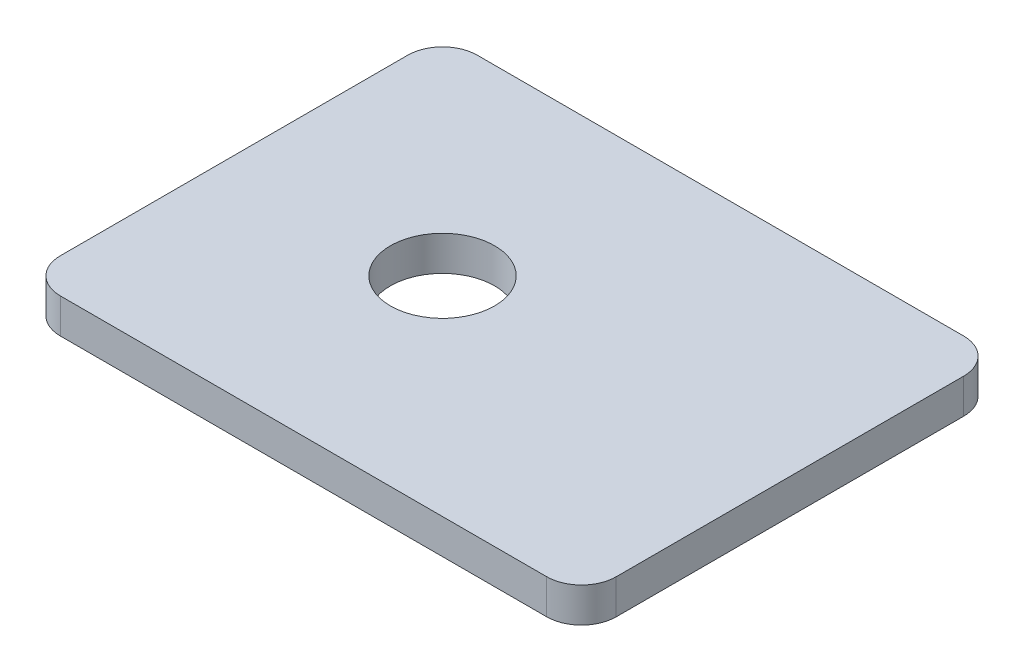
SolidWorks part; units mm, degrees
material "PE High Density"
ref_plane "Front Plane" through (0, 0, 0) normal (0, 0, 1) x (1, 0, 0)
ref_plane "Top Plane" through (0, 0, 0) normal (0, 1, 0) x (1, 0, 0)
ref_plane "Right Plane" through (0, 0, 0) normal (1, 0, 0) x (0, 0, -1)
sketch "Sketch1" plane through (0, 0, 0) normal (0, 1, 0) x (1, 0, 0)
  line L1 (3.175, 0) -> (47.625, 0)
  line L2 (0, 3.175) -> (0, 34.925)
  line L3 (3.175, 38.1) -> (47.625, 38.1)
  line L4 (50.8, 3.175) -> (50.8, 34.925)
  arc A0 (0, 34.925) -> (3.175, 38.1) centre (3.175, 34.925) cw
  arc A1 (47.625, 38.1) -> (50.8, 34.925) centre (47.625, 34.925) cw
  arc A2 (47.625, 0) -> (50.8, 3.175) centre (47.625, 3.175) ccw
  arc A3 (3.175, 0) -> (0, 3.175) centre (3.175, 3.175) cw
  point P7 (0, 38.1)
  point P12 (50.8, 0)
  point P15 (0, 0)
  dimension "D3" = 3.175
  dimension "D4" = 3.175
  dimension "D1" = 38.1
  dimension "D2" = 50.8
extrude "Boss-Extrude1" add sketch "Sketch1" along normal blind 3.175 contours L2 A0 L3 A1 L4 A2 L1 A3
hole_wizard "3/8 (0.375) Diameter Hole1" positions "Sketch2" profile "Sketch3" hole size "3/8" standard "ANSI Inch" end condition through all
sketch "Sketch2" plane through (0, 3.175, 0) normal (0, 1, 0) x (1, 0, 0)
  line L0 (0, 3.175) -> (0, 34.925) construction
  line L1 (3.175, 38.1) -> (47.625, 38.1) construction
  line L2 (3.175, 0) -> (47.625, 0) construction
  point P0 (19.05, 19.05)
  dimension "D1" = 19.05
  dimension "D2" = 19.05
  dimension "D3" = 19.05
sketch "Sketch3" plane through (19.05, 3.175, -19.05) normal (1, 0, 0) x (0, 0, 1)
  line L0 (0, 0) -> (0, 3.175)
  line L1 (0, 3.175) -> (4.7625, 3.175)
  line L2 (4.7625, 3.175) -> (4.7625, 0)
  line L5 (4.7625, 0) -> (0, 0)
  line L11 (0, -6.35) -> (0, 107.95) construction
  dimension "Thru Hole Dia." = 9.525
  dimension "Thru Hole Depth" = 3.175
